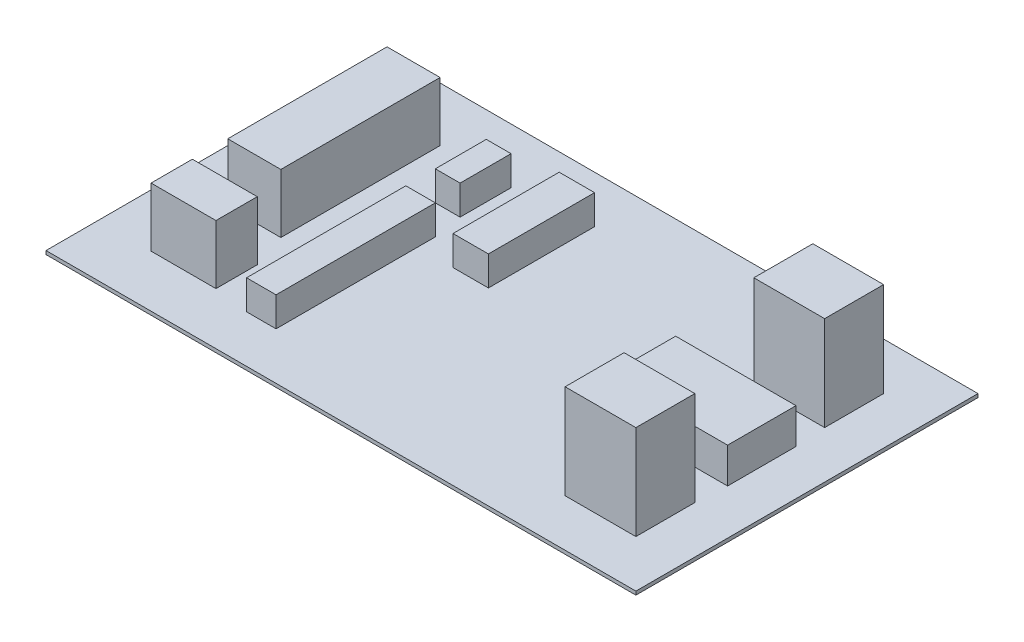
SolidWorks part; units mm, degrees
ref_plane "Front Plane" through (0, 0, 0) normal (0, 0, 1) x (1, 0, 0)
ref_plane "Top Plane" through (0, 0, 0) normal (0, 1, 0) x (1, 0, 0)
ref_plane "Right Plane" through (0, 0, 0) normal (1, 0, 0) x (0, 0, -1)
sketch "Sketch1" plane through (0, 0, 0) normal (0, 1, 0) x (1, 0, 0)
  line L1 (0, 0) -> (500, 0)
  line L2 (0, 0) -> (0, 290)
  line L3 (0, 290) -> (500, 290)
  line L4 (500, 0) -> (500, 290)
  dimension "D1" = 290
  dimension "D2" = 500
extrude "Boss-Extrude1" add sketch "Sketch1" along normal blind 3
sketch "Sketch2" plane through (0, 3, 0) normal (0, 1, 0) x (1, 0, 0)
  line L0 (20, 20) -> (480, 20)
  line L1 (480, 20) -> (480, 270)
  line L2 (480, 270) -> (20, 270)
  line L3 (20, 270) -> (20, 20)
  line L4 (0, 290) -> (0, 0)
  line L5 (0, 0) -> (500, 0)
  line L6 (500, 0) -> (500, 290)
  line L7 (500, 290) -> (0, 290)
  line L8 (0, 290) -> (0, 0)
  line L9 (0, 0) -> (500, 0)
  line L10 (500, 0) -> (500, 290)
  line L11 (500, 290) -> (0, 290)
  line L12 (340, 20) -> (340, 459.283) construction
  line L13 (280, 0) -> (280, 488.3834) construction
  line L14 (500, 145) -> (-15.9339, 145) construction
  line L15 (140.5, 221.6) -> (162.7913, 221.6) construction
  line L16 (460, 40) -> (400, 40) construction
  line L17 (460, 40) -> (460, 90) construction
  line L18 (460, 90) -> (400, 90) construction
  line L19 (400, 40) -> (400, 90) construction
  line L20 (90, 109.0645) -> (45, 109.0645) construction
  line L21 (90, 109.0645) -> (90, 244.0645) construction
  line L22 (90, 244.0645) -> (45, 244.0645) construction
  line L23 (45, 109.0645) -> (45, 244.0645) construction
  line L24 (45, 44.0645) -> (100, 44.0645)
  line L25 (45, 44.0645) -> (45, 79.0645)
  line L26 (45, 79.0645) -> (100, 79.0645)
  line L27 (100, 44.0645) -> (100, 79.0645)
  line L28 (45, 44.0645) -> (100, 79.0645) construction
  line L29 (45, 79.0645) -> (100, 44.0645) construction
  line L30 (155, 40) -> (130, 40) construction
  line L31 (155, 40) -> (155, 175) construction
  line L32 (155, 175) -> (130, 175) construction
  line L33 (130, 40) -> (130, 175) construction
  line L34 (155, 40) -> (130, 175) construction
  line L35 (155, 175) -> (130, 40) construction
  line L36 (130, 200) -> (151, 200) construction
  line L37 (130, 200) -> (130, 243.2) construction
  line L38 (130, 243.2) -> (151, 243.2) construction
  line L39 (151, 200) -> (151, 243.2) construction
  line L40 (130, 200) -> (151, 243.2) construction
  line L41 (130, 243.2) -> (151, 200) construction
  line L42 (162.7913, 221.6) -> (140.5, 221.6) construction
  line L43 (140.5, 221.6) -> (140.5, 240.0029) construction
  line L44 (460, 250) -> (460, 200) construction
  line L45 (460, 250) -> (400, 250) construction
  line L46 (400, 250) -> (400, 200) construction
  line L47 (460, 200) -> (400, 200) construction
  line L48 (200, 205) -> (200, 242.6981) construction
  line L49 (359.7332, 116) -> (461.7332, 116)
  line L50 (359.7332, 116) -> (359.7332, 174)
  line L51 (359.7332, 174) -> (461.7332, 174)
  line L52 (461.7332, 116) -> (461.7332, 174)
  line L53 (359.7332, 116) -> (461.7332, 174) construction
  line L54 (359.7332, 174) -> (461.7332, 116) construction
  line L55 (215, 160) -> (185, 160) construction
  line L56 (215, 160) -> (215, 250) construction
  line L57 (215, 250) -> (185, 250) construction
  line L58 (185, 160) -> (185, 250) construction
  line L59 (215, 160) -> (185, 250) construction
  line L60 (215, 250) -> (185, 160) construction
  line L61 (200, 242.6981) -> (200, 205) construction
  line L62 (200, 205) -> (207.742, 205) construction
  line L63 (142.5, 107.5) -> (142.5, 177.2975) construction
  line L64 (142.5, 177.2975) -> (142.5, 40) construction
  line L65 (0, 280) -> (407.3731, 280) construction
  line L66 (407.3731, 280) -> (490, 280) construction
  line L67 (490, 280) -> (490, -7.234) construction
  line L68 (490, -7.234) -> (490, 10) construction
  line L69 (490, 10) -> (-12.6094, 10) construction
  line L70 (-12.6094, 10) -> (10, 10) construction
  line L71 (10, 10) -> (10, 315.2223) construction
  line L73 (337.9263, 165.4502) -> (237.9263, 165.4502)
  line L74 (337.9263, 165.4502) -> (337.9263, 235.4502)
  line L75 (337.9263, 235.4502) -> (237.9263, 235.4502)
  line L76 (237.9263, 165.4502) -> (237.9263, 235.4502)
  circle A0 centre (400, 40) radius 2
  circle A1 centre (460, 40) radius 2
  circle A2 centre (400, 90) radius 2
  circle A3 centre (460, 90) radius 2
  circle A4 centre (132.54, 206.6) radius 1.6
  circle A5 centre (132.54, 236.6) radius 1.6
  circle A6 centre (148.46, 236.6) radius 1.6
  circle A7 centre (148.46, 206.6) radius 1.6
  circle A8 centre (400, 200) radius 2
  circle A9 centre (400, 250) radius 2
  circle A10 centre (460, 250) radius 2
  circle A11 centre (460, 200) radius 2
  circle A12 centre (190, 245) radius 3
  circle A13 centre (190, 165) radius 3
  circle A14 centre (210, 245) radius 3
  circle A15 centre (210, 165) radius 3
  circle A16 centre (142.5, 50.393) radius 2
  circle A17 centre (142.5, 61.393) radius 2
  circle A18 centre (142.5, 72.393) radius 2
  circle A19 centre (142.5, 83.393) radius 2
  circle A20 centre (142.5, 94.393) radius 2
  circle A21 centre (142.5, 105.393) radius 2
  circle A22 centre (142.5, 116.393) radius 2
  circle A23 centre (142.5, 127.393) radius 2
  circle A24 centre (142.5, 138.393) radius 2
  circle A25 centre (142.5, 149.393) radius 2
  circle A26 centre (60, 10) radius 2.5
  circle A27 centre (490, 50) radius 2.5
  circle A28 centre (60, 280) radius 2.5
  circle A29 centre (10, 50) radius 2.5
  circle A30 centre (60, 280) radius 2.5
  circle A31 centre (490, 240) radius 2.5
  circle A32 centre (10, 240) radius 2.5
  circle A33 centre (440, 10) radius 2.5
  circle A34 centre (440, 280) radius 2.5
  circle A35 centre (374.9732, 169.34) radius 2
  circle A36 centre (373.7332, 118.54) radius 2
  circle A37 centre (425.7732, 123.62) radius 2
  circle A38 centre (456.2532, 118.54) radius 2
  circle A39 centre (449.9032, 169.34) radius 2
  point P26 (72.5, 61.5645)
  point P31 (142.5, 107.5)
  point P36 (140.5, 221.6)
  point P60 (410.7332, 145)
  point P66 (200, 205)
  dimension "D9" = 4
  dimension "D10" = 4
  dimension "D11" = 4
  dimension "D12" = 4
  dimension "D25" = 3.2
  dimension "D30" = 6
  dimension "D33" = 4
  dimension "D41" = 5
  dimension "D42" = 5
  dimension "D43" = 5
  dimension "D45" = 5
  dimension "D48" = 4
  dimension "D50" = 4
  dimension "D54" = 4
  dimension "D57" = 4
  dimension "D60" = 4
  dimension "D3" = 140
  dimension "D4" = 60
  dimension "D5" = 50
  dimension "D6" = 60
  dimension "D7" = 20
  dimension "D8" = 20
  dimension "D13" = 135
  dimension "D14" = 45
  dimension "D15" = 35
  dimension "D16" = 55
  dimension "D17" = 25
  dimension "D18" = 135
  dimension "D19" = 43.2
  dimension "D20" = 21
  dimension "D21" = 20
  dimension "D22" = 25
  dimension "D23" = 6.6
  dimension "D24" = 2.54
  dimension "D26" = 58
  dimension "D27" = 102
  dimension "D28" = 90
  dimension "D29" = 30
  dimension "D31" = 5
  dimension "D32" = 5
  dimension "D35" = 20
  dimension "D36" = 10
  dimension "D37" = 10
  dimension "D38" = 10
  dimension "D39" = 60
  dimension "D40" = 50
  dimension "D44" = 50
  dimension "D46" = 60
  dimension "D47" = 20
  dimension "D49" = 15.24
  dimension "D51" = 14
  dimension "D52" = 2.54
  dimension "D53" = 50.8
  dimension "D55" = 66.04
  dimension "D56" = 7.62
  dimension "D58" = 96.52
  dimension "D59" = 2.54
  dimension "D61" = 74.93
  dimension "D62" = 50.8
  dimension "D63" = 30
  dimension "D64" = 25
  dimension "D65" = 30
  dimension "D66" = 30
  dimension "D67" = 70
  dimension "D68" = 100
  dimension "D1" = 0
  dimension "D2" = 20
  dimension "D34" = 10
sketch "Sketch3" plane through (0, 3, 0) normal (0, 1, 0) x (1, 0, 0)
  line L1 (460, 200) -> (400, 200)
  line L2 (460, 200) -> (460, 250)
  line L3 (460, 250) -> (400, 250)
  line L4 (400, 200) -> (400, 250)
  line L5 (460, 90) -> (400, 90)
  line L6 (460, 90) -> (460, 40)
  line L7 (460, 40) -> (400, 40)
  line L8 (400, 90) -> (400, 40)
extrude "Boss-Extrude2" add sketch "Sketch3" along normal blind 80
sketch "Sketch4" plane through (0, 3, 0) normal (0, 1, 0) x (1, 0, 0)
  line L1 (461.7332, 116) -> (359.7332, 116)
  line L2 (461.7332, 116) -> (461.7332, 174)
  line L3 (461.7332, 174) -> (359.7332, 174)
  line L4 (359.7332, 116) -> (359.7332, 174)
extrude "Boss-Extrude3" add sketch "Sketch4" along normal blind 30
sketch "Sketch5" plane through (0, 3, 0) normal (0, 1, 0) x (1, 0, 0)
  line L1 (215, 160) -> (185, 160)
  line L2 (215, 160) -> (215, 250)
  line L3 (215, 250) -> (185, 250)
  line L4 (185, 160) -> (185, 250)
  line L5 (151, 200) -> (130, 200)
  line L6 (151, 200) -> (151, 243.2)
  line L7 (151, 243.2) -> (130, 243.2)
  line L8 (130, 200) -> (130, 243.2)
  line L9 (155, 40) -> (130, 40)
  line L10 (155, 40) -> (155, 175)
  line L11 (155, 175) -> (130, 175)
  line L12 (130, 40) -> (130, 175)
extrude "Boss-Extrude4" add sketch "Sketch5" along normal blind 25
sketch "Sketch6" plane through (0, 3, 0) normal (0, 1, 0) x (1, 0, 0)
  line L1 (100, 44.0645) -> (45, 44.0645)
  line L2 (100, 44.0645) -> (100, 79.0645)
  line L3 (100, 79.0645) -> (45, 79.0645)
  line L4 (45, 44.0645) -> (45, 79.0645)
  line L5 (90, 109.0645) -> (45, 109.0645)
  line L6 (90, 109.0645) -> (90, 244.0645)
  line L7 (90, 244.0645) -> (45, 244.0645)
  line L8 (45, 109.0645) -> (45, 244.0645)
extrude "Boss-Extrude5" add sketch "Sketch6" along normal blind 50
